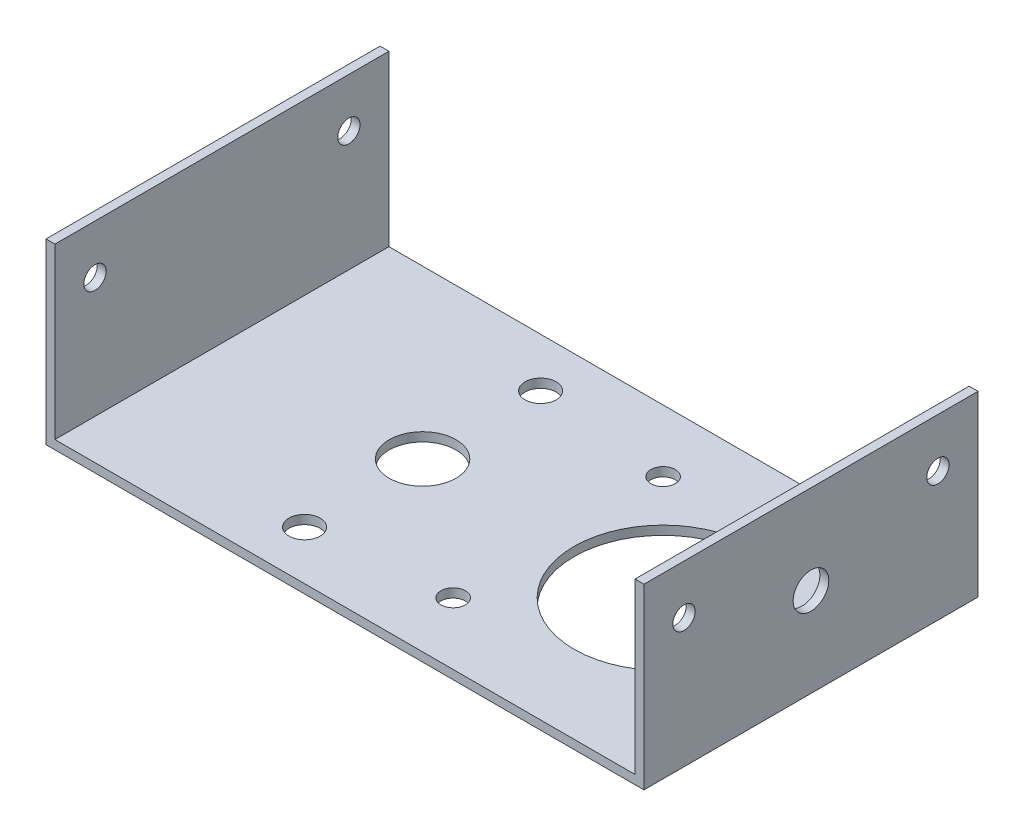
SolidWorks part; units mm, degrees
material "Liga 1060"
ref_plane "Plano frontal" through (0, 0, 0) normal (0, 0, 1) x (1, 0, 0)
ref_plane "Plano superior" through (0, 0, 0) normal (0, 1, 0) x (1, 0, 0)
ref_plane "Plano direito" through (0, 0, 0) normal (1, 0, 0) x (0, 0, -1)
sketch "Esboço1" plane through (0, 0, 0) normal (0, 1, 0) x (1, 0, 0)
  line L1 (-31.2, -37.5) -> (31.2, -37.5)
  line L2 (-31.2, -37.5) -> (-31.2, 37.5)
  line L3 (-31.2, 37.5) -> (31.2, 37.5)
  line L4 (31.2, -37.5) -> (31.2, 37.5)
  line L5 (-31.2, -37.5) -> (31.2, 37.5) construction
  line L6 (-31.2, 37.5) -> (31.2, -37.5) construction
  point P1 (0, 0)
  dimension "D1" = 62.4
  dimension "D2" = 75
extrude "Ressalto-extrusão1" add sketch "Esboço1" along normal blind 2
sketch "Esboço2" plane through (31.2, 0, 0) normal (1, 0, 0) x (0, 0, -1)
  line L0 (-37.5, 2) -> (-37.5, 0) construction
  line L1 (37.5, 0) -> (-37.5, 0)
  line L2 (37.5, 0) -> (37.5, 40)
  line L3 (37.5, 40) -> (-37.5, 40)
  line L4 (-37.5, 0) -> (-37.5, 40)
  dimension "D1" = 40
extrude "Ressalto-extrusão2" add sketch "Esboço2" along normal blind 2
mirror "Espelhar1" about plane through (0, 0, 0) normal (1, 0, 0) of "Ressalto-extrusão2"
fillet "Filete1" [suppressed] radius 5
sketch "Esboço3" plane through (-33.2, 0, 0) normal (-1, 0, 0) x (0, 0, 1)
  line L0 (-37.5, 40) -> (37.5, 40) construction
  line L1 (-37.5, 0) -> (-37.5, 40) construction
  line L2 (0, -24.75) -> (0, 24.75) construction
  circle A0 centre (-28.5, 29) radius 2.5
  circle A1 centre (28.5, 29) radius 2.5
  dimension "D1" = 5
  dimension "D2" = 11
  dimension "D3" = 9
extrude "Corte-extrusão1" cut sketch "Esboço3" against normal through all
sketch "Esboço4" plane through (0, 2, 0) normal (0, 1, 0) x (1, 0, 0)
  circle A0 centre (0, 0) radius 20
  dimension "D1" = 40
extrude "Corte-extrusão2" cut sketch "Esboço4" against normal blind 5
sketch "Esboço5" plane through (0, 2, 0) normal (0, 1, 0) x (1, 0, 0)
  circle A0 centre (23.57, 23.57) radius 2.75 construction
  circle A1 centre (23.57, -23.57) radius 2.75 construction
  circle A2 centre (-23.57, -23.57) radius 2.75 construction
  circle A3 centre (-23.57, 23.57) radius 2.75 construction
  circle A4 centre (23.57, 23.57) radius 2.75
  circle A5 centre (23.57, -23.57) radius 2.75
  circle A6 centre (-23.57, -23.57) radius 2.75
  circle A7 centre (-23.57, 23.57) radius 2.75
extrude "Corte-extrusão3" cut sketch "Esboço5" against normal through all
sketch "Esboço10" [suppressed] plane through (0, 0, 0) normal (0, 0, 1) x (1, 0, 0)
  line L0 (31.2, 16) -> (20, 2)
  line L1 (-31.2, 2) -> (31.2, 2) construction
rib "Nervura5" [suppressed] sketch "Esboço10" sketch "Esboço10" thickness 20 extrusion direction parallel to sketch draft on no parameters "D1"=20
mirror "Espelhar2" [suppressed] about plane through (0, 0, 0) normal (1, 0, 0)
sketch "Esboço11" plane through (-33.2, 0, 0) normal (-1, 0, 0) x (0, 0, 1)
  line L4 (-37.5, 40) -> (-37.5, 0)
  line L5 (-37.5, 0) -> (37.5, 0)
  line L6 (37.5, 0) -> (37.5, 40)
  line L7 (37.5, 40) -> (-37.5, 40)
  line L8 (-37.5, 40) -> (-37.5, 0)
  line L9 (-37.5, 0) -> (37.5, 0)
  line L10 (37.5, 0) -> (37.5, 40)
  line L11 (37.5, 40) -> (-37.5, 40)
  dimension "D1" = 0
extrude "Ressalto-extrusão3" add sketch "Esboço11" along normal blind 67.85
sketch "Esboço12" plane through (-31.2, 0, 0) normal (1, 0, 0) x (0, 0, -1)
  line L4 (-37.5, 2) -> (37.5, 2)
  line L5 (37.5, 2) -> (37.5, 40)
  line L6 (37.5, 40) -> (-37.5, 40)
  line L7 (-37.5, 40) -> (-37.5, 2)
  line L8 (-37.5, 2) -> (37.5, 2)
  line L9 (37.5, 2) -> (37.5, 40)
  line L10 (37.5, 40) -> (-37.5, 40)
  line L11 (-37.5, 40) -> (-37.5, 2)
  dimension "D1" = 0
extrude "Corte-extrusão4" cut sketch "Esboço12" against normal blind 67.85
sketch "Esboço13" plane through (-99.05, 0, 0) normal (1, 0, 0) x (0, 0, -1)
  circle A0 centre (28.5, 29) radius 2.5 construction
  circle A1 centre (-28.5, 29) radius 2.5 construction
  circle A2 centre (28.5, 29) radius 2.5
  circle A3 centre (-28.5, 29) radius 2.5
extrude "Corte-extrusão5" cut sketch "Esboço13" against normal blind 64.1
sketch "Esboço14" plane through (0, 2, 0) normal (0, 1, 0) x (1, 0, 0)
  circle A0 centre (-54, 0) radius 7.5 construction
  circle A1 centre (-54, 0) radius 7.5
extrude "Corte-extrusão6" cut sketch "Esboço14" against normal blind 10
sketch "Esboço16" plane through (0, 2, 0) normal (0, 1, 0) x (1, 0, 0)
  arc A0 (-57.5, 26.5) -> (-50.5, 26.5) centre (-54, 26.5) ccw construction
  arc A1 (-50.5, 26.5) -> (-57.5, 26.5) centre (-54, 26.5) ccw construction
  arc A2 (-57.5, 26.5) -> (-50.5, 26.5) centre (-54, 26.5) ccw
  arc A3 (-50.5, 26.5) -> (-57.5, 26.5) centre (-54, 26.5) ccw
  arc A4 (-50.5, -26.5) -> (-57.5, -26.5) centre (-54, -26.5) ccw construction
  arc A5 (-57.5, -26.5) -> (-50.5, -26.5) centre (-54, -26.5) ccw construction
  arc A6 (-50.5, -26.5) -> (-57.5, -26.5) centre (-54, -26.5) ccw
  arc A7 (-57.5, -26.5) -> (-50.5, -26.5) centre (-54, -26.5) ccw
extrude "Corte-extrusão7" cut sketch "Esboço16" against normal blind 10
sketch "Esboço17" plane through (31.2, 0, 0) normal (-1, 0, 0) x (0, 0, 1)
  line L0 (37.5, 40) -> (-37.5, 40) construction
  circle A0 centre (0, 20) radius 4
  dimension "D2" = 8
  dimension "D1" = 20
extrude "Corte-extrusão8" cut sketch "Esboço17" against normal blind 10
